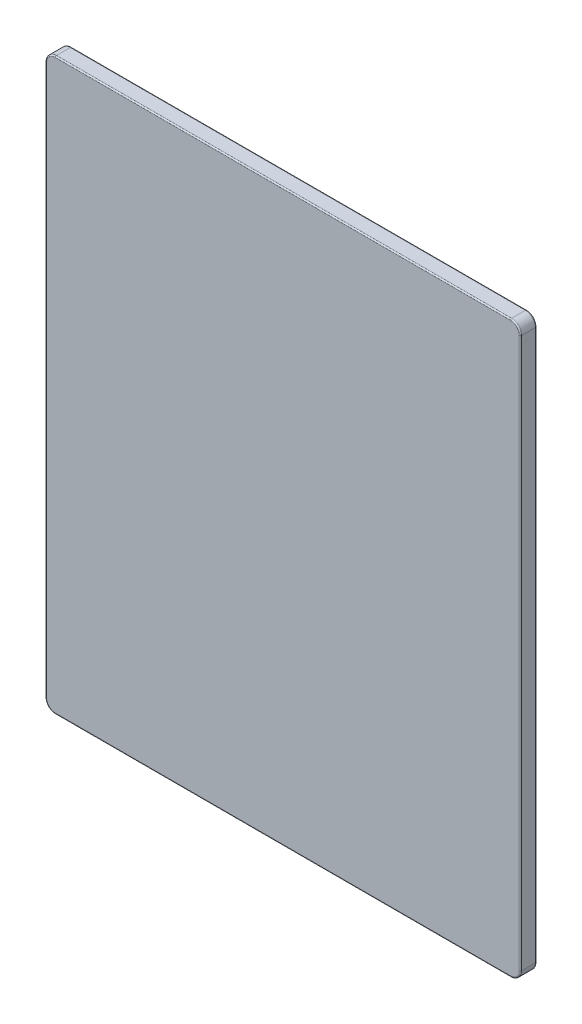
SolidWorks part; units mm, degrees
ref_plane "Front Plane" through (0, 0, 0) normal (0, 0, 1) x (1, 0, 0)
ref_plane "Top Plane" through (0, 0, 0) normal (0, 1, 0) x (1, 0, 0)
ref_plane "Right Plane" through (0, 0, 0) normal (1, 0, 0) x (0, 0, -1)
sketch "Sketch1" plane through (0, 0, 0) normal (0, 0, 1) x (1, 0, 0)
  line L1 (-190.5, -228.6) -> (190.5, -228.6)
  line L2 (-190.5, -228.6) -> (-190.5, 228.6)
  line L3 (-190.5, 228.6) -> (190.5, 228.6)
  line L4 (190.5, -228.6) -> (190.5, 228.6)
  line L5 (-190.5, -228.6) -> (190.5, 228.6) construction
  line L6 (-190.5, 228.6) -> (190.5, -228.6) construction
  point P0 (0, 0)
  dimension "D1" = 457.2
  dimension "D2" = 381
extrude "Boss-Extrude1" add sketch "Sketch1" along normal blind 13
fillet "Fillet1" radius 8 4 edges at (190.5, 228.6, 6.5) (-190.5, 228.6, 6.5) (190.5, -228.6, 6.5) (-190.5, -228.6, 6.5)
fillet "Fillet2" radius 1 16 edges at (-188.1569, 226.2569, 0) (-190.5, 0, 0) (-188.1569, -226.2569, 0) (0, -228.6, 0) (188.1569, -226.2569, 0) (190.5, 0, 0) (188.1569, 226.2569, 0) (0, 228.6, 0) (188.1569, -226.2569, 13) (0, -228.6, 13) (-188.1569, -226.2569, 13) (-190.5, 0, 13) (-188.1569, 226.2569, 13) (0, 228.6, 13) (188.1569, 226.2569, 13) (190.5, 0, 13)
